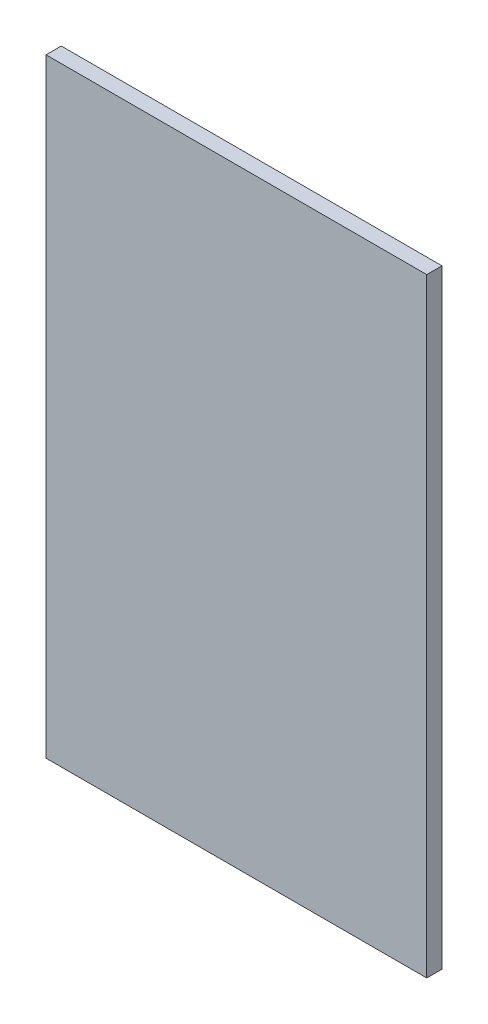
SolidWorks part; units mm, degrees
ref_plane "Alzado" through (0, 0, 0) normal (0, 0, 1) x (1, 0, 0)
ref_plane "Planta" through (0, 0, 0) normal (0, 1, 0) x (1, 0, 0)
ref_plane "Vista lateral" through (0, 0, 0) normal (1, 0, 0) x (0, 0, -1)
sketch "Croquis1" plane through (0, 0, 0) normal (0, 0, 1) x (1, 0, 0)
  line L1 (25, -40) -> (-25, -40)
  line L2 (25, -40) -> (25, 40)
  line L3 (25, 40) -> (-25, 40)
  line L4 (-25, -40) -> (-25, 40)
  line L5 (25, -40) -> (-25, 40) construction
  line L6 (25, 40) -> (-25, -40) construction
  point P0 (0, 0)
  dimension "D1" = 80
  dimension "D2" = 50
extrude "Saliente-Extruir1" add sketch "Croquis1" along normal blind 2
